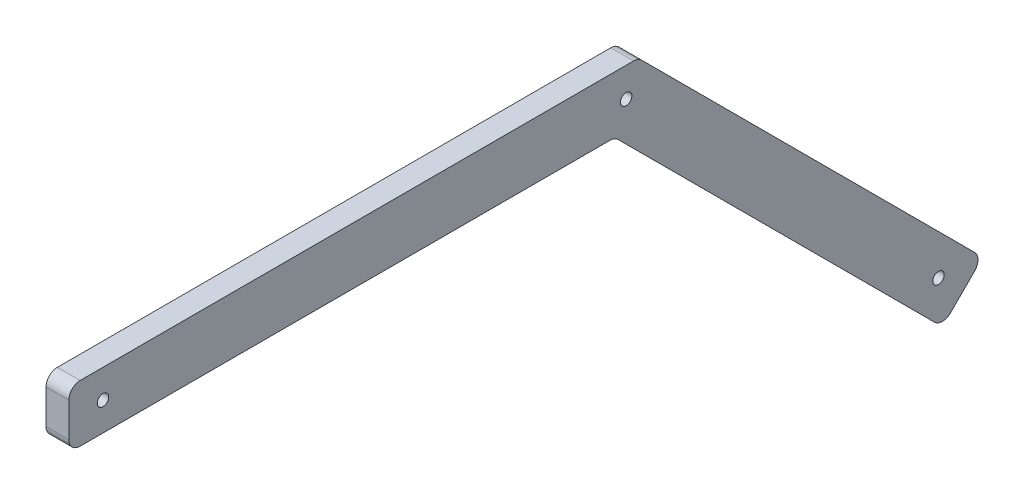
SolidWorks part; units mm, degrees
ref_plane "Front Plane" through (0, 0, 0) normal (0, 0, 1) x (1, 0, 0)
ref_plane "Top Plane" through (0, 0, 0) normal (0, 1, 0) x (1, 0, 0)
ref_plane "Right Plane" through (0, 0, 0) normal (1, 0, 0) x (0, 0, -1)
sketch "Sketch1" plane through (0, 0, 0) normal (1, 0, 0) x (0, 0, -1)
  line L0 (500, 50) -> (802.3677, -252.3677)
  line L1 (0, 0) -> (479.2893, 0)
  line L2 (0, 0) -> (0, 50)
  line L3 (0, 50) -> (500, 50)
  line L5 (500, 50) -> (802.3677, -252.3677)
  line L7 (802.3677, -252.3677) -> (767.0123, -287.723)
  line L8 (479.2893, 0) -> (767.0123, -287.723)
  dimension "D1" = 50
  dimension "D2" = 500
  dimension "D3" = 135
  dimension "D4" = 90
  dimension "D5" = 50
extrude "Boss-Extrude1" add sketch "Sketch1" along normal blind 20 contours L1 L8 L7 L0 L3 L2
fillet "Fillet1" radius 10 6 edges at (10, 0, -479.2893) (10, 50, -500) (10, -287.723, -767.0123) (10, -252.3677, -802.3677) (10, 0, 0) (10, 50, 0)
sketch "Sketch2" plane through (20, 0, 0) normal (1, 0, 0) x (0, 0, -1)
  line L0 (0, 10) -> (0, 40) construction
  circle A0 centre (30, 25) radius 5
  dimension "D2" = 10
  dimension "D1" = 30
extrude "Cut-Extrude1" cut sketch "Sketch2" against normal blind 20
sketch "Sketch3" plane through (20, 0, 0) normal (1, 0, 0) x (0, 0, -1)
  line L0 (795.2966, -259.4387) -> (774.0834, -280.6519) construction
  circle A0 centre (763.4768, -248.8321) radius 5
  dimension "D2" = 10
  dimension "D1" = 30
extrude "Cut-Extrude2" cut sketch "Sketch3" against normal blind 20
sketch "Sketch4" plane through (20, 0, 0) normal (1, 0, 0) x (0, 0, -1)
  line L0 (478.974, -0.7612) -> (499.6847, 49.2388) construction
  arc A0 (482.2183, -2.9289) -> (475.1472, 0) centre (475.1472, -10) ccw construction
  arc A1 (502.9289, 47.0711) -> (495.8579, 50) centre (495.8579, 40) ccw construction
  circle A2 centre (489.3294, 24.2388) radius 5
  dimension "D1" = 10
extrude "Cut-Extrude3" cut sketch "Sketch4" against normal blind 20
